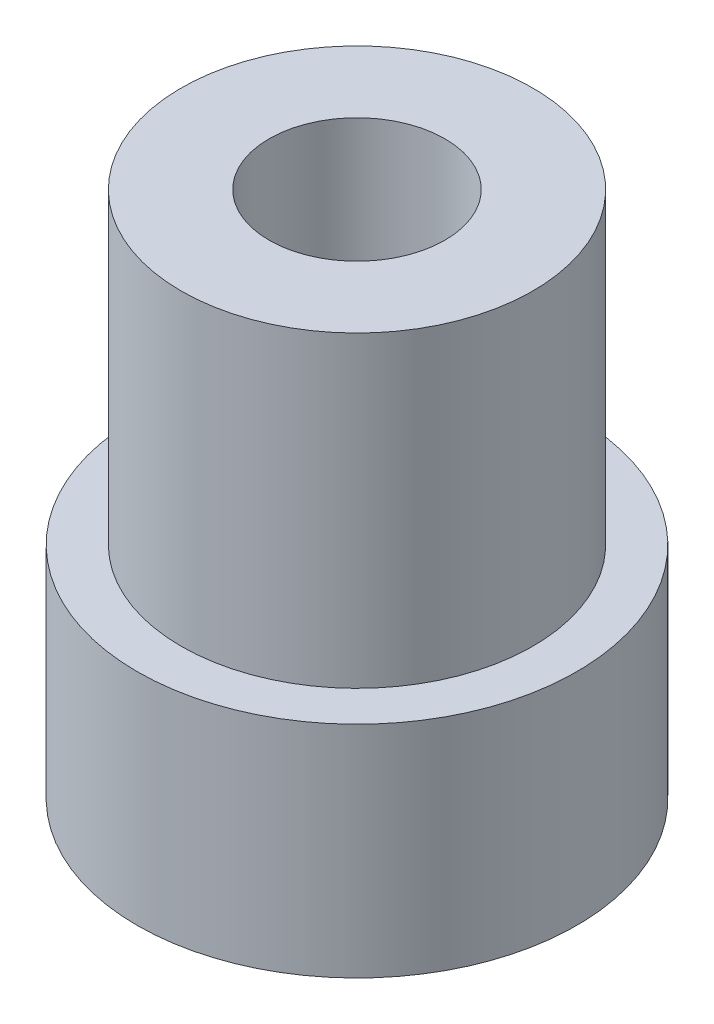
SolidWorks part; units mm, degrees
ref_plane "Front Plane" through (0, 0, 0) normal (0, 0, 1) x (1, 0, 0)
ref_plane "Top Plane" through (0, 0, 0) normal (0, 1, 0) x (1, 0, 0)
ref_plane "Right Plane" through (0, 0, 0) normal (1, 0, 0) x (0, 0, -1)
sketch "Sketch2" plane through (0, 0, 0) normal (0, 1, 0) x (1, 0, 0)
  circle A0 centre (0, 0) radius 4
  dimension "D1" = 8
extrude "Boss-Extrude1" add sketch "Sketch2" along normal blind 7
sketch "Sketch3" plane through (0, 0, 0) normal (0, -1, 0) x (1, 0, 0)
  circle A0 centre (0, 0) radius 5
  dimension "D1" = 10
extrude "Boss-Extrude2" add sketch "Sketch3" along normal blind 5
chamfer "Chamfer1" [suppressed] distance 0.5 angle 45
sketch "Sketch4" plane through (0, 7, 0) normal (0, 1, 0) x (1, 0, 0)
  circle A0 centre (0, 0) radius 1.65
  dimension "D1" = 3.3
extrude "Cut-Extrude1" cut sketch "Sketch4" against normal up to surface (12 mm away) up to face at (0, -5, -5)
sketch "Sketch5" plane through (0, 7, 0) normal (0, -1, 0) x (1, 0, 0)
  circle A0 centre (0, 0) radius 2
  dimension "D1" = 4
extrude "Cut-Extrude2" cut sketch "Sketch5" along normal blind 5
